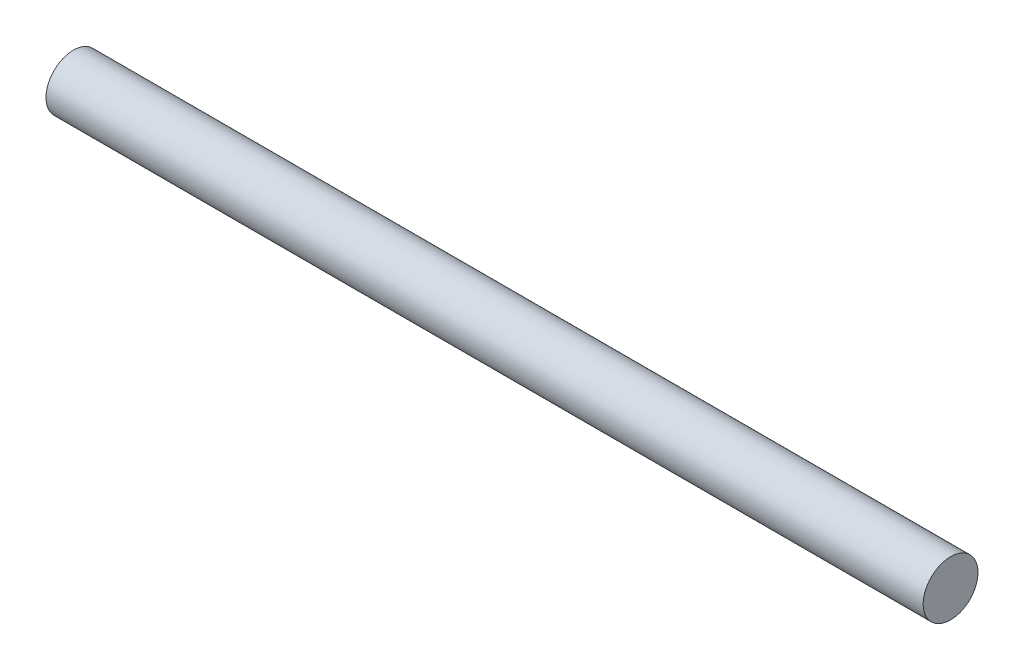
SolidWorks part; units mm, degrees
ref_plane "Front Plane" through (0, 0, 0) normal (0, 0, 1) x (1, 0, 0)
ref_plane "Top Plane" through (0, 0, 0) normal (0, 1, 0) x (1, 0, 0)
ref_plane "Right Plane" through (0, 0, 0) normal (1, 0, 0) x (0, 0, -1)
sketch "Sketch1" plane through (0, 0, 0) normal (1, 0, 0) x (0, 0, -1)
  circle A0 centre (0, 0) radius 3.175
  dimension "D1" = 6.35
extrude "Boss-Extrude1" add sketch "Sketch1" along normal blind 101.6
